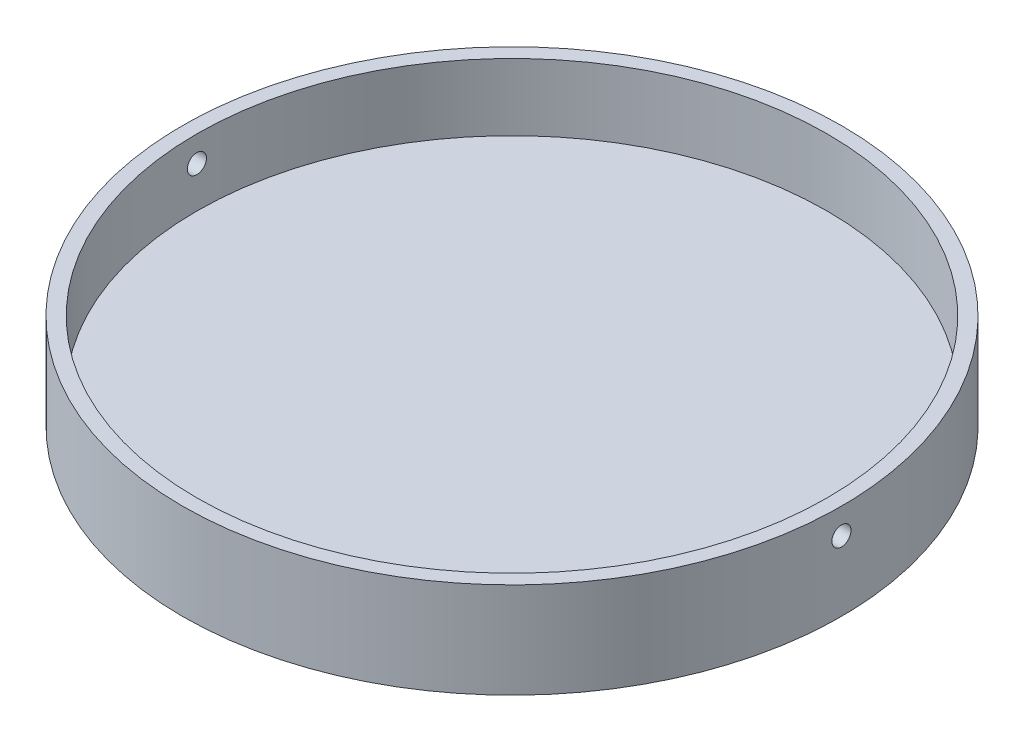
SolidWorks part; units mm, degrees
ref_plane "Front Plane" through (0, 0, 0) normal (0, 0, 1) x (1, 0, 0)
ref_plane "Top Plane" through (0, 0, 0) normal (0, 1, 0) x (1, 0, 0)
ref_plane "Right Plane" through (0, 0, 0) normal (1, 0, 0) x (0, 0, -1)
sketch "Sketch1" plane through (0, 0, 0) normal (0, 1, 0) x (1, 0, 0)
  circle A0 centre (0, 0) radius 34.5
  dimension "D1" = 69
extrude "Boss-Extrude1" add sketch "Sketch1" along normal blind 10
sketch "Sketch2" plane through (0, 10, 0) normal (0, 1, 0) x (1, 0, 0)
  circle A0 centre (0, 0) radius 33
  dimension "D1" = 66
extrude "Cut-Extrude1" cut sketch "Sketch2" against normal blind 7
ref_plane "Plane1" through (-36.085, 0, 0) normal (1, 0, 0) x (0, 0, -1)
sketch "Sketch3" plane through (-36.085, 0, 0) normal (1, 0, 0) x (0, 0, -1)
  line L0 (0, 3) -> (0, 7.3) construction
  line L3 (33, 3) -> (-33, 3) construction
  circle A0 centre (0, 7.3) radius 1
  dimension "D2" = 2
  dimension "D1" = 4.3
extrude "Cut-Extrude2" cut sketch "Sketch3" against normal through all both and the other way through all
